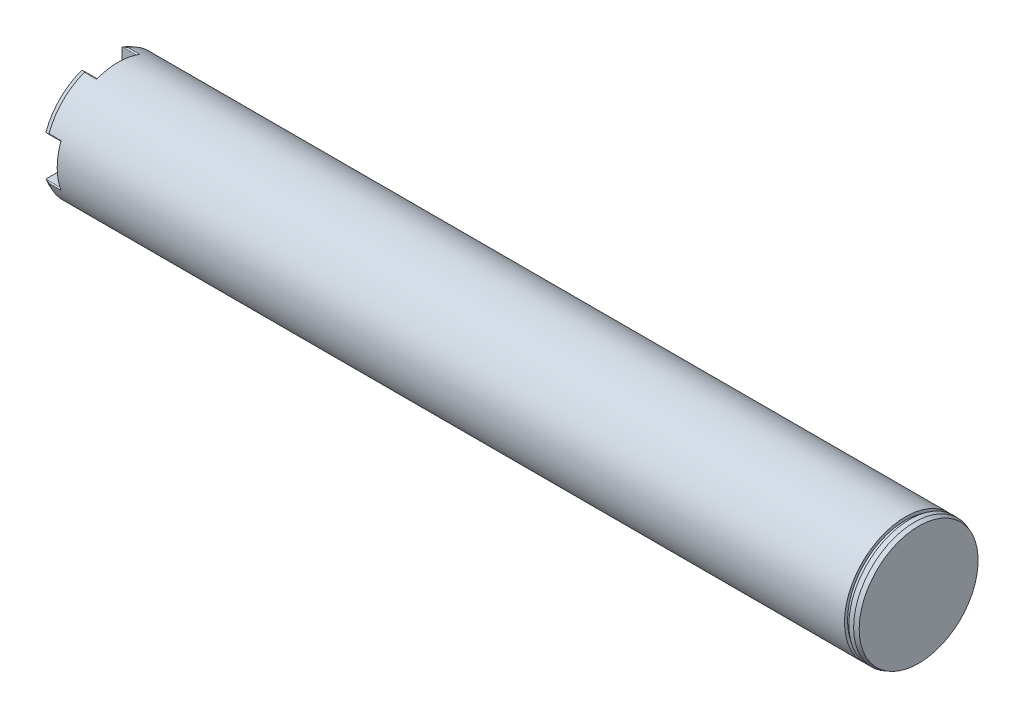
SolidWorks part; units mm, degrees
ref_plane "Front" through (0, 0, 0) normal (0, 0, 1) x (1, 0, 0)
ref_plane "Top" through (0, 0, 0) normal (0, 1, 0) x (1, 0, 0)
ref_plane "Right" through (0, 0, 0) normal (1, 0, 0) x (0, 0, -1)
sketch "Sketch1" plane through (0, 0, 0) normal (0, 0, 1) x (1, 0, 0)
  line L0 (-283, 0) -> (11.2597, 0) construction
  line L1 (-201, 20) -> (-201, 29.2721)
  line L2 (-201, 20) -> (-193, 20)
  line L3 (-193, 20) -> (-193, 8.5)
  line L4 (-199, 30) -> (0, 30)
  line L5 (0, -32.8854) -> (0, 30) construction
  line L6 (196.65, 30) -> (196.65, 28.5)
  line L7 (196.65, 28.5) -> (194.5, 28.5)
  line L8 (201, 0) -> (201, 29.2721)
  line L9 (-146.794, 0) -> (201, 0)
  line L10 (-201, 29.2721) -> (-199, 30)
  line L11 (201, 29.2721) -> (199, 30)
  line L12 (0, 30) -> (194.5, 30)
  line L13 (194.5, 28.5) -> (194.5, 30)
  line L14 (196.65, 30) -> (199, 30)
  line L16 (-193, 8.5) -> (-183, 8.5)
  line L17 (-183, 8.5) -> (-182.0987, 7)
  line L18 (-182.0987, 7) -> (-151, 7)
  line L19 (-151, 7) -> (-146.794, 0)
  dimension "D1" = 402
  dimension "D2" = 2
  dimension "D3" = 8
  dimension "D4" = 40
  dimension "D5" = 60
  dimension "D6" = 20
  dimension "D7" = 17
  dimension "D8" = 6.5
  dimension "D9" = 2.15
  dimension "D10" = 14
  dimension "D11" = 59
  dimension "D12" = 59
  dimension "D13" = 10
  dimension "D14" = 42
  dimension "D15" = 57
  dimension "D16" = 201
revolve "Base-Revolve" add sketch "Sketch1" angle 360 about L0
cosmetic thread "Cosmetic Thread2" parameters "D1"=24.1, "D2"=16
sketch "Sketch3" plane through (-201, 0, 0) normal (-1, 0, 0) x (0, 0, 1)
  line L0 (0, 0) -> (30, 0) construction
  line L1 (0, 0) -> (0, 30) construction
  line L2 (10, 28.2843) -> (10, 17.3205)
  line L3 (-10, 28.2843) -> (-10, 17.3205)
  line L4 (17.3205, 10) -> (28.2843, 10)
  line L5 (17.3205, -10) -> (28.2843, -10)
  line L6 (-17.3205, -10) -> (-28.2843, -10)
  line L7 (-17.3205, 10) -> (-28.2843, 10)
  line L8 (-10, -28.2843) -> (-10, -17.3205)
  line L9 (10, -28.2843) -> (10, -17.3205)
  circle A0 centre (0, 0) radius 20 construction
  circle A1 centre (0, 0) radius 30 construction
  arc A2 (17.3205, -10) -> (17.3205, 10) centre (0, 0) ccw
  arc A3 (28.2843, -10) -> (28.2843, 10) centre (0, 0) ccw
  arc A4 (-10, -17.3205) -> (10, -17.3205) centre (0, 0) ccw
  arc A5 (-10, -28.2843) -> (10, -28.2843) centre (0, 0) ccw
  arc A6 (-28.2843, 10) -> (-28.2843, -10) centre (0, 0) ccw
  arc A7 (-17.3205, 10) -> (-17.3205, -10) centre (0, 0) ccw
  arc A8 (10, 17.3205) -> (-10, 17.3205) centre (0, 0) ccw
  arc A9 (10, 28.2843) -> (-10, 28.2843) centre (0, 0) ccw
  dimension "D1" = 20
  dimension "D2" = 20
extrude "Affræsning" cut sketch "Sketch3" against normal blind 8
fillet "R0.5 rundinger" radius 0.5 20 edges at (-196, 28.2843, -10) (-196, 28.2843, 10) (-197, 17.3205, 10) (-197, 17.3205, -10) (-197, -10, 17.3205) (-197, 10, 17.3205) (-196, 10, 28.2843) (-196, -10, 28.2843) (-197, 10, -17.3205) (-197, -10, -17.3205) (-196, -10, -28.2843) (-196, 10, -28.2843) (-196, -28.2843, 10) (-196, -28.2843, -10) (-197, -17.3205, -10) (-197, -17.3205, 10)
